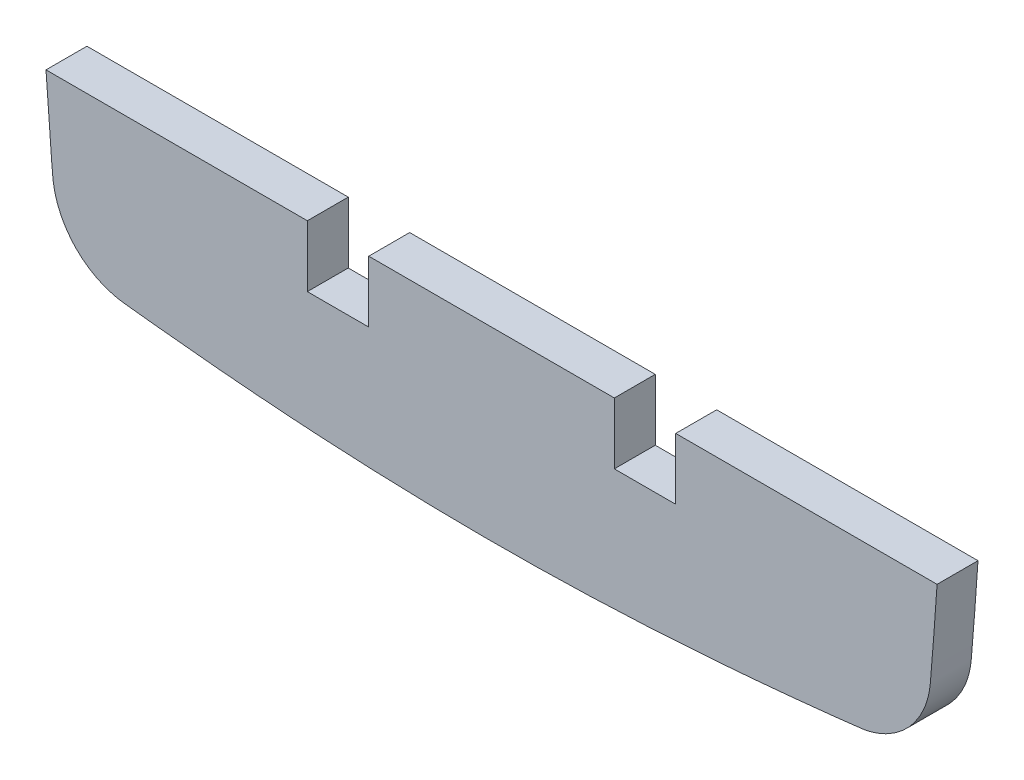
SolidWorks part; units mm, degrees
material "Beech"
ref_plane "Front Plane" through (0, 0, 0) normal (0, 0, 1) x (1, 0, 0)
ref_plane "Top Plane" through (0, 0, 0) normal (0, 1, 0) x (1, 0, 0)
ref_plane "Right Plane" through (0, 0, 0) normal (1, 0, 0) x (0, 0, -1)
sketch "Sketch1" plane through (0, 0, 0) normal (0, 0, 1) x (1, 0, 0)
  line L0 (0, 0) -> (63.5, 0) construction
  line L1 (63.5, 58.9764) -> (63.5, 0) construction
  line L2 (63.5, 0) -> (63.5, -61.125) construction
  line L3 (63.5, 0) -> (120.0842, 0) construction
  line L4 (8.2053, -38.1) -> (118.7947, -38.1)
  line L5 (78.74, -38.1) -> (78.74, -45.72)
  line L6 (40.64, -38.1) -> (48.26, -38.1)
  line L7 (40.64, -38.1) -> (40.64, -45.72)
  line L8 (40.64, -45.72) -> (48.26, -45.72)
  line L9 (48.26, -38.1) -> (48.26, -45.72)
  line L10 (86.36, -45.72) -> (78.74, -45.72)
  line L11 (86.36, -38.1) -> (86.36, -45.72)
  line L12 (86.36, -38.1) -> (78.74, -38.1)
  spline S0 degree 3 poles (63.5, 58.9764) (67.6826, 58.9764) (71.957, 58.9025) (76.319, 58.7475) (78.5001, 58.6699) (80.703, 58.5721) (82.9274, 58.4536) (84.0395, 58.3943) (85.1571, 58.3299) (86.2799, 58.2602) (86.8413, 58.2253) (87.404, 58.1891) (87.968, 58.1517) (88.25, 58.1329) (88.5324, 58.1138) (88.8151, 58.0944) (88.9564, 58.0848) (89.0978, 58.075) (89.3101, 58.0602) (89.3808, 58.0552) (89.487, 58.0478) (89.5224, 58.0453) (89.5755, 58.0415) (89.5932, 58.0403) (89.6286, 58.0378) (89.6482, 58.0364) (89.6641, 58.0353) (93.7153, 57.7485) (97.8895, 57.3901) (102.1839, 56.9565) (104.3311, 56.7396) (106.5084, 56.504) (108.7158, 56.2497) (108.9917, 56.2179) (109.2678, 56.1875) (109.8221, 56.1191) (110.1012, 56.0723) (110.381, 56.0127) (110.9404, 55.8935) (111.5021, 55.7228) (112.6047, 55.2727) (113.1456, 54.9922) (113.6629, 54.6588) (113.9216, 54.4921) (114.1743, 54.3124) (114.4195, 54.1203) (114.542, 54.0243) (114.6627, 53.9252) (114.8406, 53.772) (114.8993, 53.7203) (114.9866, 53.6415) (115.0156, 53.615) (115.0588, 53.5751) (115.0731, 53.5617) (115.0946, 53.5416) (115.1018, 53.5349) (115.1161, 53.5214) (115.1245, 53.5135) (115.1304, 53.5079) (115.8844, 52.7944) (116.5392, 51.9444) (117.5621, 50.0753) (117.9244, 49.0571) (118.1257, 48.0189) (118.176, 47.7594) (118.2164, 47.4986) (118.2774, 46.9768) (118.2951, 46.7164) (118.3144, 46.4549) (118.3531, 45.9318) (118.3915, 45.4049) (118.4296, 44.8742) (118.5058, 43.8126) (118.5808, 42.7356) (118.6542, 41.6431) (118.8009, 39.4582) (118.9415, 37.2112) (119.0735, 34.9024) (119.1395, 33.748) (119.2033, 32.5782) (119.2647, 31.3929) (119.2954, 30.8003) (119.3254, 30.2038) (119.3548, 29.6035) (119.3695, 29.3033) (119.384, 29.0022) (119.3984, 28.7001) (119.4056, 28.5491) (119.4127, 28.3978) (119.4234, 28.1705) (119.4269, 28.0947) (119.4322, 27.9809) (119.4339, 27.9429) (119.4366, 27.8859) (119.4375, 27.867) (119.4388, 27.8385) (119.4392, 27.829) (119.4399, 27.8147) (119.4401, 27.81) (119.4405, 27.8005) (119.4408, 27.7942) (119.441, 27.791) (119.5907, 24.5434) (119.7438, 20.7009) (119.865, 16.2601) (119.9256, 14.0397) (119.978, 11.6699) (120.0165, 9.1513) (120.0357, 7.8921) (120.0515, 6.5957) (120.0629, 5.2623) (120.0686, 4.5956) (120.0733, 3.9197) (120.0768, 3.2346) (120.0785, 2.892) (120.08, 2.5471) (120.0811, 2.2) (120.0817, 2.0264) (120.0822, 1.8523) (120.0828, 1.5902) (120.083, 1.5027) (120.0832, 1.3712) (120.0833, 1.3273) (120.0834, 1.2615) (120.0835, 1.2395) (120.0835, 1.2066) (120.0835, 1.1956) (120.0836, 1.1791) (120.0836, 1.1736) (120.0836, 1.1626) (120.0836, 1.1589) (120.0836, 1.1516) (120.0891, -2.5763) (120.0585, -5.55) (120.0271, -7.7697) (120.0114, -8.8795) (119.9952, -9.801) (119.9812, -10.5346) (119.9743, -10.9014) (119.9678, -11.2212) (119.9622, -11.4941) (119.9594, -11.6305) (119.9567, -11.7552) (119.9531, -11.9246) (119.952, -11.9782) (119.9503, -12.0541) (119.9498, -12.0787) (119.949, -12.1145) (119.9487, -12.1262) (119.9484, -12.1436) (119.9482, -12.1493) (119.9481, -12.1578) (119.948, -12.1606) (119.9479, -12.1649) (119.9479, -12.1663) (119.9478, -12.1684) (119.9478, -12.1691) (119.9478, -12.1705) (119.9478, -12.1694) (119.9477, -12.1719) (119.8924, -14.6989) (119.8237, -17.072) (119.7473, -19.2912) (119.7092, -20.4008) (119.6691, -21.472) (119.6278, -22.5048) (119.6071, -23.0212) (119.5862, -23.528) (119.565, -24.0252) (119.5544, -24.2738) (119.5437, -24.52) (119.533, -24.7638) (119.5276, -24.8857) (119.5223, -25.0071) (119.5142, -25.1881) (119.5115, -25.2483) (119.5075, -25.3384) (119.5061, -25.3684) (119.5041, -25.4134) (119.5034, -25.4283) (119.5024, -25.4508) (119.5021, -25.4582) (119.5015, -25.4695) (119.5014, -25.4732) (119.501, -25.4807) (119.5009, -25.4832) (119.5007, -25.4881) (119.2734, -30.5188) (118.9944, -35.244) (118.6885, -39.6635) (118.5355, -41.8732) (118.3758, -44.0066) (118.2121, -46.0644) (118.1303, -47.0933) (118.0474, -48.1033) (117.9638, -49.0944) (117.9221, -49.59) (117.8442, -50.0862) (117.7307, -50.5754) (117.674, -50.8199) (117.6084, -51.0628) (117.534, -51.303) (117.4968, -51.4231) (117.4574, -51.5425) (117.395, -51.7205) (117.3736, -51.7797) (117.3408, -51.8681) (117.3297, -51.8975) (117.3129, -51.9416) (117.3073, -51.9562) (117.2988, -51.9782) (117.2959, -51.9855) (117.2902, -52.0002) (117.2881, -52.0056) (117.2845, -52.0148) (116.8227, -53.1914) (116.1296, -54.2956) (114.4065, -56.1487) (113.3758, -56.8961) (112.2874, -57.4199) (111.7432, -57.6818) (111.1844, -57.8882) (110.6239, -58.0423) (110.3436, -58.1193) (110.063, -58.1833) (109.7834, -58.2345) (109.6436, -58.2601) (109.5041, -58.2825) (109.226, -58.3211) (109.0876, -58.3365) (108.9493, -58.3524) (107.8425, -58.4798) (106.7449, -58.6025) (105.6566, -58.7206) (103.4799, -58.9568) (101.34, -59.1743) (99.2368, -59.3732) (98.1852, -59.4727) (97.1427, -59.5675) (96.1094, -59.6577) (95.5928, -59.7028) (95.0784, -59.7468) (94.5664, -59.7896) (94.3104, -59.8111) (94.0549, -59.8322) (93.8, -59.853) (93.6726, -59.8635) (93.5453, -59.8738) (93.3546, -59.8892) (93.291, -59.8944) (93.1958, -59.902) (93.164, -59.9046) (93.1164, -59.9084) (93.1006, -59.9096) (93.0768, -59.9116) (93.0688, -59.9122) (93.053, -59.9135) (93.0463, -59.914) (93.0371, -59.9147) (88.3396, -60.2902) (83.7418, -60.5763) (79.2458, -60.7747) (76.9978, -60.874) (74.7753, -60.9515) (72.5787, -61.0079) (71.4804, -61.0361) (70.3885, -61.0591) (69.3032, -61.077) (68.7605, -61.086) (68.2195, -61.0937) (67.6801, -61.1001) (67.4103, -61.1033) (67.141, -61.1062) (66.6033, -61.1113) (66.3361, -61.1136) (66.0667, -61.1156) (63.9118, -61.1314) (61.7279, -61.1274) (57.3171, -61.0775) (55.0887, -61.0315) (50.5863, -60.8959) (48.3124, -60.8061) (46.0161, -60.6939) (44.8679, -60.6378) (43.7142, -60.5761) (42.5548, -60.5088) (41.9752, -60.4752) (41.3941, -60.4401) (40.8117, -60.4036) (40.5205, -60.3854) (40.2289, -60.3668) (39.937, -60.3478) (39.7911, -60.3384) (39.645, -60.3288) (39.4258, -60.3143) (39.3527, -60.3095) (39.2431, -60.3022) (39.2065, -60.2997) (39.1517, -60.2961) (39.1334, -60.2948) (39.0968, -60.2924) (39.0765, -60.291) (39.0603, -60.2899) (34.9056, -60.0109) (30.6113, -59.6556) (26.1788, -59.2205) (23.9625, -59.003) (21.7115, -58.7657) (19.4256, -58.5088) (19.1399, -58.4767) (18.8536, -58.4442) (18.5668, -58.4115) (18.4234, -58.3952) (18.2798, -58.3787) (17.9924, -58.3457) (17.8487, -58.3302) (17.7045, -58.3112) (17.1274, -58.2354) (16.542, -58.1056) (15.3822, -57.7319) (14.8077, -57.4875) (14.2533, -57.1836) (13.9761, -57.0317) (13.7039, -56.8652) (13.4386, -56.6849) (13.306, -56.5948) (13.175, -56.5012) (12.9816, -56.3559) (12.9176, -56.3066) (12.8224, -56.2314) (12.7908, -56.2061) (12.7436, -56.1679) (12.7279, -56.1551) (12.7044, -56.1359) (12.6966, -56.1294) (12.681, -56.1165) (12.6717, -56.1088) (12.6654, -56.1036) (12.262, -55.7689) (11.88, -55.3985) (11.1759, -54.5931) (10.8532, -54.1587) (10.2781, -53.2409) (10.0257, -52.7575) (9.6031, -51.7577) (9.4325, -51.2413) (9.1738, -50.1928) (9.0857, -49.6606) (8.9927, -48.5993) (8.9499, -48.0647) (8.9058, -47.5255) (8.8175, -46.4471) (8.7305, -45.3511) (8.6452, -44.2374) (8.4745, -42.0099) (8.3102, -39.7117) (8.1553, -37.3424) (8.0779, -36.1578) (8.0028, -34.9554) (7.9305, -33.7353) (7.8943, -33.1252) (7.8588, -32.5107) (7.824, -31.8918) (7.8066, -31.5823) (7.7894, -31.2717) (7.7724, -30.9601) (7.7639, -30.8042) (7.7554, -30.6481) (7.7428, -30.4135) (7.7386, -30.3352) (7.7323, -30.2177) (7.7302, -30.1786) (7.7271, -30.1198) (7.7261, -30.1001) (7.7245, -30.0707) (7.724, -30.0609) (7.723, -30.0413) (7.7223, -30.0296) (7.7219, -30.0217) (7.6153, -28.0098) (7.5122, -25.8692) (7.417, -23.5991) (7.3695, -22.464) (7.3239, -21.2966) (7.2809, -20.0967) (7.2595, -19.4968) (7.2386, -18.8887) (7.2185, -18.2726) (7.2085, -17.9645) (7.1986, -17.6545) (7.189, -17.3423) (7.1841, -17.1863) (7.1793, -17.0297) (7.1722, -16.7941) (7.1699, -16.7155) (7.1664, -16.5973) (7.1652, -16.5578) (7.1635, -16.4987) (7.1629, -16.4789) (7.162, -16.4493) (7.1617, -16.4394) (7.1613, -16.4246) (7.1611, -16.4197) (7.1608, -16.4098) (7.1606, -16.403) (7.1605, -16.3999) (7.1147, -14.8356) (7.0645, -12.9185) (7.0209, -10.6468) (6.9991, -9.5109) (6.979, -8.2863) (6.9622, -6.973) (6.9538, -6.3164) (6.9463, -5.6375) (6.9399, -4.9365) (6.9366, -4.586) (6.9337, -4.23) (6.931, -3.8684) (6.9297, -3.6876) (6.9285, -3.5054) (6.9267, -3.23) (6.9262, -3.1379) (6.9254, -2.9992) (6.9251, -2.9528) (6.9246, -2.86) (6.9243, -2.8153) (6.9241, -2.7669) (6.9074, 0.3256) (6.9177, 3.0099) (6.9373, 5.2829) (6.9471, 6.4195) (6.9593, 7.4533) (6.9723, 8.3843) (6.9788, 8.8498) (6.9854, 9.2897) (6.9922, 9.7038) (6.9955, 9.9109) (6.9989, 10.1115) (7.0039, 10.4029) (7.0056, 10.4984) (7.0081, 10.6393) (7.0089, 10.6858) (7.0101, 10.7551) (7.0105, 10.778) (7.0112, 10.8123) (7.0114, 10.8238) (7.0117, 10.8408) (7.0118, 10.8465) (7.0119, 10.855) (7.012, 10.8579) (7.0121, 10.8636) (7.0121, 10.8643) (7.0122, 10.8692) (7.0583, 13.4041) (7.1185, 15.8078) (7.1873, 18.0796) (7.2218, 19.2155) (7.2584, 20.3184) (7.2967, 21.3884) (7.3158, 21.9234) (7.3354, 22.4501) (7.3553, 22.9686) (7.3652, 23.2279) (7.3753, 23.4851) (7.3854, 23.7402) (7.3904, 23.8678) (7.3955, 23.9948) (7.4031, 24.1846) (7.4057, 24.2478) (7.4095, 24.3423) (7.4108, 24.3738) (7.4127, 24.4209) (7.4133, 24.4366) (7.4143, 24.4602) (7.4146, 24.468) (7.4153, 24.4837) (7.4155, 24.4895) (7.4159, 24.4994) (7.6225, 29.5566) (7.8794, 34.3389) (8.1635, 38.8427) (8.3055, 41.0946) (8.4544, 43.2771) (8.6076, 45.3902) (8.6267, 45.6544) (8.646, 45.9174) (8.6845, 46.4414) (8.7011, 46.7019) (8.7246, 46.9623) (8.7715, 47.4831) (8.858, 48.0044) (9.1092, 49.031) (9.2739, 49.5363) (9.4771, 50.0256) (9.5787, 50.2703) (9.69, 50.511) (9.8104, 50.7468) (9.8705, 50.8648) (9.9329, 50.9814) (10.0298, 51.1545) (10.0627, 51.2118) (10.1127, 51.2973) (10.1295, 51.3257) (10.1549, 51.3682) (10.1634, 51.3823) (10.1762, 51.4035) (10.1805, 51.4106) (10.1891, 51.4247) (10.1923, 51.43) (10.1977, 51.4387) (10.5404, 51.9993) (10.9366, 52.5271) (11.8187, 53.4893) (12.3052, 53.9232) (13.3381, 54.6836) (13.8845, 55.0101) (15.0077, 55.5438) (15.5846, 55.7518) (16.1625, 55.904) (16.4515, 55.9801) (16.7407, 56.0423) (17.3164, 56.1395) (17.6021, 56.1707) (17.8874, 56.2038) (18.4579, 56.27) (19.0263, 56.335) (19.5927, 56.3987) (20.7253, 56.526) (21.8495, 56.6484) (22.9653, 56.7657) (25.1969, 57.0003) (27.3948, 57.2148) (29.5588, 57.4095) (30.6408, 57.5068) (31.7143, 57.5992) (32.7793, 57.6867) (33.3117, 57.7304) (33.8421, 57.7729) (34.3703, 57.8143) (34.6344, 57.8349) (34.898, 57.8553) (35.161, 57.8753) (35.2925, 57.8854) (35.4239, 57.8953) (35.6208, 57.9101) (35.6864, 57.9151) (35.7847, 57.9224) (35.8175, 57.9249) (35.8666, 57.9285) (35.883, 57.9297) (35.9076, 57.9316) (35.9158, 57.9322) (35.9321, 57.9334) (35.9392, 57.9339) (35.9485, 57.9346) (40.733, 58.2901) (45.4244, 58.5517) (54.6114, 58.8949) (59.107, 58.9764) (63.5, 58.9764) (67.6826, 58.9764) (71.957, 58.9025) knots -0.004464 0 0 0 0.004464 0.004464 0.004464 0.008929 0.008929 0.008929 0.013393 0.013393 0.013393 0.017857 0.017857 0.017857 0.022321 0.022321 0.022321 0.026786 0.026786 0.03125 0.03125 0.035714 0.035714 0.040179 0.040179 0.044643 0.044643 0.044643 0.049107 0.049107 0.049107 0.053571 0.053571 0.053571 0.058036 0.058036 0.0625 0.0625 0.0625 0.066964 0.066964 0.071429 0.071429 0.071429 0.075893 0.075893 0.075893 0.080357 0.080357 0.084821 0.084821 0.089286 0.089286 0.09375 0.09375 0.098214 0.098214 0.102679 0.102679 0.102679 0.107143 0.107143 0.111607 0.111607 0.111607 0.116071 0.116071 0.120536 0.120536 0.120536 0.125 0.125 0.125 0.129464 0.129464 0.129464 0.133929 0.133929 0.133929 0.138393 0.138393 0.138393 0.142857 0.142857 0.142857 0.147321 0.147321 0.147321 0.151786 0.151786 0.15625 0.15625 0.160714 0.160714 0.165179 0.165179 0.169643 0.169643 0.174107 0.174107 0.178571 0.178571 0.178571 0.183036 0.183036 0.183036 0.1875 0.1875 0.1875 0.191964 0.191964 0.191964 0.196429 0.196429 0.196429 0.200893 0.200893 0.200893 0.205357 0.205357 0.209821 0.209821 0.214286 0.214286 0.21875 0.21875 0.223214 0.223214 0.227679 0.227679 0.232143 0.232143 0.232143 0.236607 0.236607 0.236607 0.241071 0.241071 0.241071 0.245536 0.245536 0.245536 0.25 0.25 0.254464 0.254464 0.258929 0.258929 0.263393 0.263393 0.267857 0.267857 0.272321 0.272321 0.276786 0.276786 0.28125 0.28125 0.285714 0.285714 0.285714 0.290179 0.290179 0.290179 0.294643 0.294643 0.294643 0.299107 0.299107 0.299107 0.303571 0.303571 0.303571 0.308036 0.308036 0.3125 0.3125 0.316964 0.316964 0.321429 0.321429 0.325893 0.325893 0.330357 0.330357 0.334821 0.334821 0.334821 0.339286 0.339286 0.339286 0.34375 0.34375 0.34375 0.348214 0.348214 0.348214 0.352679 0.352679 0.352679 0.357143 0.357143 0.357143 0.361607 0.361607 0.366071 0.366071 0.370536 0.370536 0.375 0.375 0.379464 0.379464 0.383929 0.383929 0.383929 0.388393 0.388393 0.392857 0.392857 0.392857 0.397321 0.397321 0.397321 0.401786 0.401786 0.401786 0.40625 0.40625 0.410714 0.410714 0.410714 0.415179 0.415179 0.415179 0.419643 0.419643 0.419643 0.424107 0.424107 0.424107 0.428571 0.428571 0.428571 0.433036 0.433036 0.433036 0.4375 0.4375 0.441964 0.441964 0.446429 0.446429 0.450893 0.450893 0.455357 0.455357 0.459821 0.459821 0.459821 0.464286 0.464286 0.464286 0.46875 0.46875 0.46875 0.473214 0.473214 0.473214 0.477679 0.477679 0.477679 0.482143 0.482143 0.486607 0.486607 0.486607 0.491071 0.491071 0.495536 0.495536 0.5 0.5 0.5 0.504464 0.504464 0.504464 0.508929 0.508929 0.508929 0.513393 0.513393 0.513393 0.517857 0.517857 0.522321 0.522321 0.526786 0.526786 0.53125 0.53125 0.535714 0.535714 0.535714 0.540179 0.540179 0.540179 0.544643 0.544643 0.544643 0.549107 0.549107 0.549107 0.553571 0.553571 0.558036 0.558036 0.558036 0.5625 0.5625 0.566964 0.566964 0.566964 0.571429 0.571429 0.571429 0.575893 0.575893 0.580357 0.580357 0.584821 0.584821 0.589286 0.589286 0.59375 0.59375 0.598214 0.598214 0.598214 0.602679 0.602679 0.607143 0.607143 0.611607 0.611607 0.616071 0.616071 0.620536 0.620536 0.625 0.625 0.625 0.629464 0.629464 0.629464 0.633929 0.633929 0.633929 0.638393 0.638393 0.638393 0.642857 0.642857 0.642857 0.647321 0.647321 0.647321 0.651786 0.651786 0.65625 0.65625 0.660714 0.660714 0.665179 0.665179 0.669643 0.669643 0.674107 0.674107 0.674107 0.678571 0.678571 0.678571 0.683036 0.683036 0.683036 0.6875 0.6875 0.6875 0.691964 0.691964 0.691964 0.696429 0.696429 0.700893 0.700893 0.705357 0.705357 0.709821 0.709821 0.714286 0.714286 0.71875 0.71875 0.723214 0.723214 0.723214 0.727679 0.727679 0.727679 0.732143 0.732143 0.732143 0.736607 0.736607 0.736607 0.741071 0.741071 0.741071 0.745536 0.745536 0.75 0.75 0.754464 0.754464 0.758929 0.758929 0.758929 0.763393 0.763393 0.763393 0.767857 0.767857 0.767857 0.772321 0.772321 0.772321 0.776786 0.776786 0.78125 0.78125 0.785714 0.785714 0.790179 0.790179 0.794643 0.794643 0.799107 0.799107 0.803571 0.803571 0.808036 0.808036 0.808036 0.8125 0.8125 0.8125 0.816964 0.816964 0.816964 0.821429 0.821429 0.821429 0.825893 0.825893 0.825893 0.830357 0.830357 0.834821 0.834821 0.839286 0.839286 0.84375 0.84375 0.848214 0.848214 0.852679 0.852679 0.852679 0.857143 0.857143 0.857143 0.861607 0.861607 0.861607 0.866071 0.866071 0.870536 0.870536 0.870536 0.875 0.875 0.879464 0.879464 0.879464 0.883929 0.883929 0.883929 0.888393 0.888393 0.892857 0.892857 0.897321 0.897321 0.901786 0.901786 0.90625 0.90625 0.910714 0.910714 0.910714 0.915179 0.915179 0.919643 0.919643 0.924107 0.924107 0.928571 0.928571 0.928571 0.933036 0.933036 0.9375 0.9375 0.9375 0.941964 0.941964 0.941964 0.946429 0.946429 0.946429 0.950893 0.950893 0.950893 0.955357 0.955357 0.955357 0.959821 0.959821 0.959821 0.964286 0.964286 0.964286 0.96875 0.96875 0.973214 0.973214 0.977679 0.977679 0.982143 0.982143 0.986607 0.986607 0.991071 0.991071 0.991071 0.995536 0.995536 1 1 1 1.004464 1.004464 1.004464 only from (63.5, 58.9764) to (63.5, 58.9764)
  point P3 (6.9158, 0)
  dimension "D1" = 58.9764
  dimension "D2" = 63.5
  dimension "D3" = 61.125
  dimension "D4" = 56.5842
  dimension "D5" = 38.1
  dimension "D6" = 7.62
  dimension "D7" = 7.62
  dimension "D8" = 15.24
extrude "Boss-Extrude1" add sketch "Sketch1" along normal blind 5.08 contours S0 L4 L11 L10 L5 L9 L8 L7
